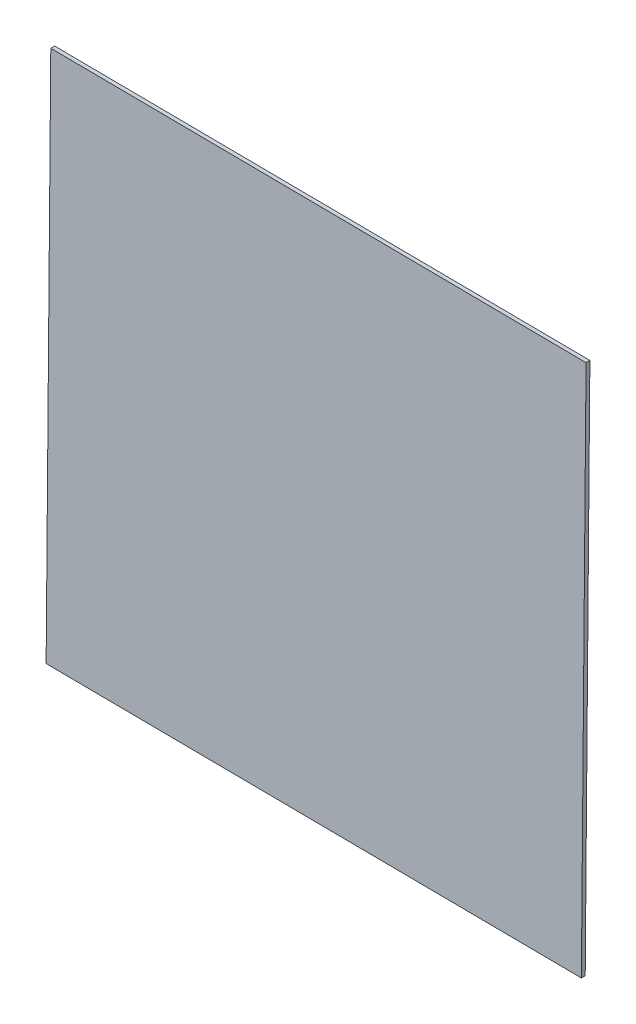
SolidWorks part; units mm, degrees
material "PE Low Density Film"
ref_plane "Front Plane" through (0, 0, 0) normal (0, 0, 1) x (1, 0, 0)
ref_plane "Top Plane" through (0, 0, 0) normal (0, 1, 0) x (1, 0, 0)
ref_plane "Right Plane" through (0, 0, 0) normal (1, 0, 0) x (0, 0, -1)
sketch "Sketch1" plane through (0, 0, 0) normal (0, 0, 1) x (1, 0, 0)
  line L4 (-97.5599, 73.9656) -> (-97.7146, 56.2371)
  line L5 (-97.7146, 56.2371) -> (-79.9861, 56.0824)
  line L6 (-79.9861, 56.0824) -> (-79.8314, 73.8109)
  line L7 (-79.8314, 73.8109) -> (-97.5599, 73.9656)
  line L8 (-97.5599, 73.9656) -> (-97.7146, 56.2371)
  line L9 (-97.7146, 56.2371) -> (-79.9861, 56.0824)
  line L10 (-79.9861, 56.0824) -> (-79.8314, 73.8109)
  line L11 (-79.8314, 73.8109) -> (-97.5599, 73.9656)
  dimension "D1" = 0
extrude "Boss-Extrude1" add sketch "Sketch1" along normal blind 0.127
